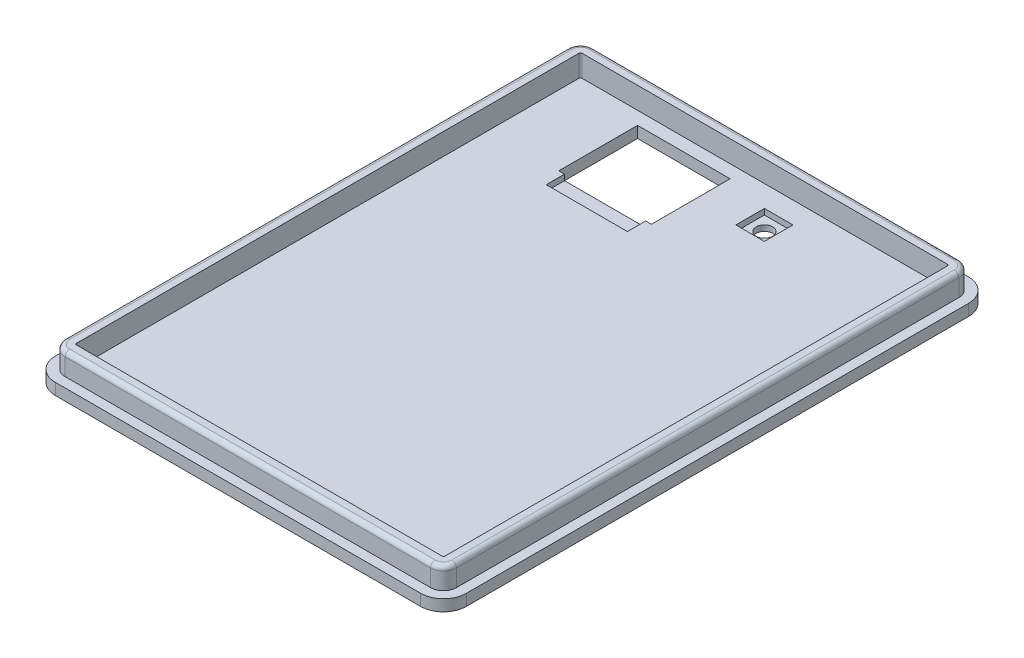
SolidWorks part; units mm, degrees
ref_plane "Front Plane" through (0, 0, 0) normal (0, 0, 1) x (1, 0, 0)
ref_plane "Top Plane" through (0, 0, 0) normal (0, 1, 0) x (1, 0, 0)
ref_plane "Right Plane" through (0, 0, 0) normal (1, 0, 0) x (0, 0, -1)
sketch "Sketch1" plane through (0, 0, 0) normal (0, 1, 0) x (1, 0, 0)
  line L1 (0, 0) -> (180, 0)
  line L2 (0, 0) -> (0, 240)
  line L3 (0, 240) -> (180, 240)
  line L4 (180, 0) -> (180, 240)
  dimension "D1" = 180
  dimension "D2" = 240
extrude "Boss-Extrude1" add sketch "Sketch1" along normal blind 5
sketch "Sketch2" plane through (0, 0, 0) normal (0, -1, 0) x (1, 0, 0)
  line L1 (40, -225) -> (80.55, -225)
  line L2 (40, -225) -> (40, -190.5)
  line L3 (40, -190.5) -> (80.55, -190.5)
  line L4 (80.55, -225) -> (80.55, -190.5)
  line L5 (180, -240) -> (0, -240) construction
  line L6 (0, -240) -> (0, 0) construction
  circle A0 centre (105.55, -215) radius 3.6
  dimension "D3" = 7.2
  dimension "D1" = 40.55
  dimension "D2" = 34.5
  dimension "D4" = 15
  dimension "D5" = 40
  dimension "D6" = 25
  dimension "D7" = 25
extrude "Cut-Extrude1" cut sketch "Sketch2" against normal through all
sketch "Sketch3" plane through (0, 5, 0) normal (0, 1, 0) x (1, 0, 0)
  line L1 (111.8, 221.25) -> (99.3, 221.25)
  line L2 (111.8, 221.25) -> (111.8, 208.75)
  line L3 (111.8, 208.75) -> (99.3, 208.75)
  line L4 (99.3, 221.25) -> (99.3, 208.75)
  line L5 (111.8, 221.25) -> (99.3, 208.75) construction
  line L6 (111.8, 208.75) -> (99.3, 221.25) construction
  point P0 (105.55, 215)
  dimension "D1" = 12.5
extrude "Cut-Extrude2" cut sketch "Sketch3" against normal blind 2.5
sketch "Sketch4" plane through (0, 5, 0) normal (0, 1, 0) x (1, 0, 0)
  line L0 (80.55, 190.5) -> (40, 190.5) construction
  line L1 (78.05, 190.5) -> (42.5, 190.5)
  line L2 (78.05, 190.5) -> (78.05, 182.5)
  line L3 (78.05, 182.5) -> (42.5, 182.5)
  line L4 (42.5, 190.5) -> (42.5, 182.5)
  line L5 (40, 190.5) -> (40, 225) construction
  line L6 (80.55, 225) -> (80.55, 190.5) construction
  dimension "D1" = 2.5
  dimension "D2" = 2.5
  dimension "D3" = 8
extrude "Cut-Extrude3" cut sketch "Sketch4" against normal blind 2.5
fillet "Fillet1" radius 10 4 edges at (180, 2.5, -240) (180, 2.5, 0) (0, 2.5, 0) (0, 2.5, -240)
sketch "Sketch5" plane through (0, 0, 0) normal (0, -1, 0) x (1, 0, 0)
  line L0 (90, 0) -> (90, -20) construction
  line L1 (26, -20) -> (154, -20)
  line L2 (25, -21) -> (25, -22)
  line L3 (26, -23) -> (154, -23)
  line L4 (155, -21) -> (155, -22)
  line L5 (10, 0) -> (170, 0) construction
  line L6 (25, -33) -> (25, -34)
  line L7 (26, -32) -> (154, -32)
  line L8 (155, -33) -> (155, -34)
  line L9 (26, -35) -> (154, -35)
  line L10 (25, -45) -> (25, -46)
  line L11 (26, -44) -> (154, -44)
  line L12 (155, -45) -> (155, -46)
  line L13 (26, -47) -> (154, -47)
  line L14 (25, -57) -> (25, -58)
  line L15 (26, -56) -> (154, -56)
  line L16 (155, -57) -> (155, -58)
  line L17 (26, -59) -> (154, -59)
  line L18 (25, -69) -> (25, -70)
  line L19 (26, -68) -> (154, -68)
  line L20 (155, -69) -> (155, -70)
  line L21 (26, -71) -> (154, -71)
  line L22 (25, -81) -> (25, -82)
  line L23 (26, -80) -> (154, -80)
  line L24 (155, -81) -> (155, -82)
  line L25 (26, -83) -> (154, -83)
  arc A0 (154, -20) -> (155, -21) centre (154, -21) cw
  arc A1 (154, -23) -> (155, -22) centre (154, -22) ccw
  arc A2 (25, -22) -> (26, -23) centre (26, -22) ccw
  arc A3 (25, -21) -> (26, -20) centre (26, -21) cw
  arc A4 (25, -33) -> (26, -32) centre (26, -33) cw
  arc A5 (25, -34) -> (26, -35) centre (26, -34) ccw
  arc A6 (154, -32) -> (155, -33) centre (154, -33) cw
  arc A7 (154, -35) -> (155, -34) centre (154, -34) ccw
  arc A8 (25, -45) -> (26, -44) centre (26, -45) cw
  arc A9 (25, -46) -> (26, -47) centre (26, -46) ccw
  arc A10 (154, -44) -> (155, -45) centre (154, -45) cw
  arc A11 (154, -47) -> (155, -46) centre (154, -46) ccw
  arc A12 (25, -57) -> (26, -56) centre (26, -57) cw
  arc A13 (25, -58) -> (26, -59) centre (26, -58) ccw
  arc A14 (154, -56) -> (155, -57) centre (154, -57) cw
  arc A15 (154, -59) -> (155, -58) centre (154, -58) ccw
  arc A16 (25, -69) -> (26, -68) centre (26, -69) cw
  arc A17 (25, -70) -> (26, -71) centre (26, -70) ccw
  arc A18 (154, -68) -> (155, -69) centre (154, -69) cw
  arc A19 (154, -71) -> (155, -70) centre (154, -70) ccw
  arc A20 (25, -81) -> (26, -80) centre (26, -81) cw
  arc A21 (25, -82) -> (26, -83) centre (26, -82) ccw
  arc A22 (154, -80) -> (155, -81) centre (154, -81) cw
  arc A23 (154, -83) -> (155, -82) centre (154, -82) ccw
  point P11 (155, -20)
  point P14 (155, -23)
  point P17 (25, -23)
  dimension "D4" = 1
  dimension "D1" = 20
  dimension "D2" = 3
  dimension "D3" = 130
  dimension "D6" = 9
  dimension "D5" = 6
extrude "Cut-Extrude4" [suppressed] cut sketch "Sketch5" against normal through all
sketch "Sketch6" plane through (0, 5, 0) normal (0, 1, 0) x (1, 0, 0)
  line L0 (175.7, 10) -> (175.7, 230)
  line L1 (170, 235.7) -> (10, 235.7)
  line L2 (4.3, 230) -> (4.3, 10)
  line L3 (10, 4.3) -> (170, 4.3)
  line L4 (180, 10) -> (180, 230)
  line L5 (170, 240) -> (10, 240)
  line L6 (0, 230) -> (0, 10)
  line L7 (10, 0) -> (170, 0)
  line L8 (180, 10) -> (180, 230) construction
  line L9 (170, 240) -> (10, 240) construction
  line L10 (0, 230) -> (0, 10) construction
  line L11 (10, 0) -> (170, 0) construction
  line L12 (170.7, 10) -> (170.7, 230)
  line L13 (170, 230.7) -> (10, 230.7)
  line L14 (9.3, 230) -> (9.3, 10)
  line L15 (10, 9.3) -> (170, 9.3)
  arc A0 (175.7, 230) -> (170, 235.7) centre (170, 230) ccw
  arc A1 (10, 235.7) -> (4.3, 230) centre (10, 230) ccw
  arc A2 (4.3, 10) -> (10, 4.3) centre (10, 10) ccw
  arc A3 (170, 4.3) -> (175.7, 10) centre (170, 10) ccw
  arc A4 (180, 230) -> (170, 240) centre (170, 230) ccw
  arc A5 (10, 240) -> (0, 230) centre (10, 230) ccw
  arc A6 (0, 10) -> (10, 0) centre (10, 10) ccw
  arc A7 (170, 0) -> (180, 10) centre (170, 10) ccw
  arc A8 (180, 230) -> (170, 240) centre (170, 230) ccw construction
  arc A9 (10, 240) -> (0, 230) centre (10, 230) ccw construction
  arc A10 (0, 10) -> (10, 0) centre (10, 10) ccw construction
  arc A11 (170, 0) -> (180, 10) centre (170, 10) ccw construction
  arc A12 (170.7, 230) -> (170, 230.7) centre (170, 230) ccw
  arc A13 (10, 230.7) -> (9.3, 230) centre (10, 230) ccw
  arc A14 (9.3, 10) -> (10, 9.3) centre (10, 10) ccw
  arc A15 (170, 9.3) -> (170.7, 10) centre (170, 10) ccw
  dimension "D1" = 0
  dimension "D2" = 4.3
  dimension "D3" = 5
extrude "Boss-Extrude2" add sketch "Sketch6" along normal blind 9.5
fillet "Fillet2" radius 2 8 edges at (175.7, 14.5, -120) (174.0305, 14.5, -5.9695) (90, 14.5, -4.3) (5.9695, 14.5, -5.9695) (4.3, 14.5, -120) (5.9695, 14.5, -234.0305) (90, 14.5, -235.7) (174.0305, 14.5, -234.0305)
